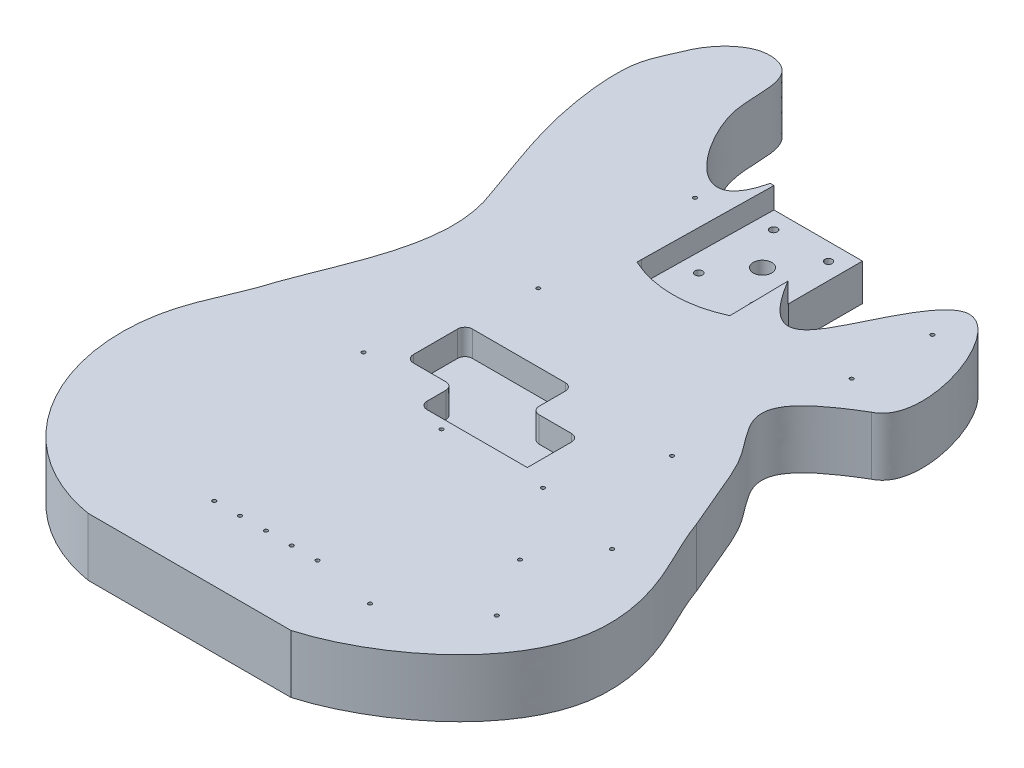
SolidWorks part; units mm, degrees
ref_plane "Front Plane" through (0, 0, 0) normal (0, 0, 1) x (1, 0, 0)
ref_plane "Top Plane" through (0, 0, 0) normal (0, 1, 0) x (1, 0, 0)
ref_plane "Right Plane" through (0, 0, 0) normal (1, 0, 0) x (0, 0, -1)
sketch "Sketch1" plane through (0, 0, 0) normal (0, 1, 0) x (1, 0, 0)
  line L0 (-31.75, 431.8) -> (31.75, 431.8)
  line L1 (-69.85, 0) -> (69.85, 0)
  line L2 (31.75, 431.8) -> (31.75, 381)
  line L3 (0, 431.8) -> (0, 0) construction
  spline S0 degree 3 poles (-69.85, 0) (-122.7459, 8.8946) (-170.3738, 68.3736) (-165.5312, 154.7593) (-147.8347, 185.8105) (-142.875, 203.2) knots 0 0 0 0 0.581043 0.783837 1 1 1 1
  spline S1 degree 3 poles (-142.875, 203.2) (-128.6398, 243.0991) (-104.4904, 285.9502) (-122.2248, 330.2) knots 0 0 0 0 1 1 1 1
  spline S2 degree 3 poles (-122.2248, 330.2) (-131.7635, 357.8566) (-146.2426, 392.3515) (-152.7726, 455.2781) (-144.5433, 471.0132) (-135.4704, 492.8612) (-120.6511, 508.7509) (-90.8297, 507.3178) (-88.3646, 481.7202) (-88.7047, 444.4419) (-43.0115, 384.6457) (-31.75, 431.8) knots 0 0 0 0 0.228271 0.373681 0.455315 0.473382 0.545352 0.564859 0.659458 0.744201 1 1 1 1
  spline S3 degree 3 poles (69.85, 0) (111.9348, 12.1111) (186.0145, 65.7497) (170.8416, 155.4983) (152.3381, 185.6263) (146.05, 203.2) knots 0 0 0 0 0.586136 0.784814 1 1 1 1
  spline S4 degree 3 poles (146.05, 203.2) (136.1599, 225.6504) (132.5896, 236.8474) (120.3836, 260.933) (109.5687, 273.3596) (96.5902, 297.0243) (109.0963, 311.9927) (139.7, 330.2) knots 0 0 0 0 0.33898 0.396393 0.554386 0.616722 1 1 1 1
  spline S5 degree 3 poles (139.7, 330.2) (166.4459, 342.892) (123.5038, 464.5308) (76.8127, 369.3895) (59.5093, 333.6668) (31.75, 381) knots 0 0 0 0 0.451982 0.679896 1 1 1 1
  point P5 (0, 412.75)
  point P7 (0, 0)
  point P10 (0, 50.8)
  point P11 (0, 101.6)
  point P12 (0, 152.4)
  point P13 (0, 177.8)
  point P15 (0, 203.2)
  point P17 (0, 254)
  point P18 (0, 279.4)
  point P19 (0, 330.2)
  point P20 (0, 406.4)
  point P21 (0, 381)
  point P22 (0, 482.6)
  point P23 (0, 508)
  point P24 (0, 457.2)
  point P25 (0, 355.6)
  point P38 (0, 422.275)
  dimension "D5" = 50.8
  dimension "D35" = 149.225
  dimension "D42" = 139.7
  dimension "D1" = 63.5
  dimension "D2" = 139.7
  dimension "D4" = 431.8
  dimension "D6" = 101.6
  dimension "D7" = 152.4
  dimension "D8" = 177.8
  dimension "D9" = 203.2
  dimension "D10" = 254
  dimension "D11" = 279.4
  dimension "D12" = 330.2
  dimension "D13" = 381
  dimension "D14" = 406.4
  dimension "D15" = 457.2
  dimension "D16" = 482.6
  dimension "D17" = 508
  dimension "D18" = 146.05
  dimension "D19" = 165.1
  dimension "D20" = 161.925
  dimension "D21" = 152.4
  dimension "D22" = 142.875
  dimension "D23" = 123.825
  dimension "D24" = 117.475
  dimension "D25" = 122.2248
  dimension "D26" = 139.7
  dimension "D27" = 146.05
  dimension "D28" = 149.225
  dimension "D29" = 139.7
  dimension "D30" = 107.95
  dimension "D31" = 88.9
  dimension "D32" = 85.725
  dimension "D33" = 6.35
  dimension "D34" = 53.975
  dimension "D36" = 174.625
  dimension "D37" = 168.275
  dimension "D38" = 157.1498
  dimension "D39" = 146.05
  dimension "D40" = 123.825
  dimension "D41" = 106.3498
  dimension "D43" = 355.6
  dimension "D44" = 422.275
  dimension "D45" = 146.05
  dimension "D46" = 114.3
  dimension "D47" = 82.55
  dimension "D48" = 66.675
extrude "Boss-Extrude1" add sketch "Sketch1" along normal blind 40.005
sketch "Sketch2" plane through (0, 40.005, 0) normal (0, 1, 0) x (1, 0, 0)
  line L0 (-29.21, 431.8) -> (31.75, 431.8)
  line L1 (31.75, 431.8) -> (-31.75, 431.8) construction
  line L2 (31.75, 381) -> (31.75, 431.8) construction
  line L3 (-29.21, 431.8) -> (-30.6832, 341.9475)
  line L4 (31.75, 431.8) -> (33.2232, 341.9475)
  line L5 (1.27, 431.8) -> (1.27, 340.7706) construction
  line L6 (-30.6832, 341.9475) -> (33.2232, 341.9475) construction
  line L7 (33.2232, 341.9475) -> (33.2232, 338.8995)
  line L8 (-30.6832, 341.9475) -> (-30.6832, 338.8995)
  line L9 (1.27, 407.1241) -> (1.27, 331.7875) construction
  arc A0 (-30.6832, 338.8995) -> (33.2232, 338.8995) centre (1.27, 407.1241) ccw
  point P13 (1.27, 341.9475)
  dimension "D5" = 7.112
  dimension "D1" = 60.96
  dimension "D2" = 89.8525
  dimension "D3" = 63.9064
  dimension "D4" = 3.048
extrude "Cut-Extrude1" cut sketch "Sketch2" against normal blind 14.605
sketch "Sketch3" plane through (0, 25.4, 0) normal (0, 1, 0) x (1, 0, 0)
  line L0 (1.27, 431.8) -> (1.27, 393.3952) construction
  line L1 (31.75, 431.8) -> (-29.21, 431.8) construction
  line L2 (31.75, 381) -> (31.75, 431.8) construction
  line L5 (33.2232, 341.9475) -> (32.6067, 379.5515) construction
  line L6 (-29.21, 431.8) -> (-30.6832, 341.9475) construction
  circle A0 centre (1.27, 393.3952) radius 6.35
  circle A1 centre (-17.526, 419.862) radius 2.54
  circle A2 centre (20.2692, 419.862) radius 2.54
  circle A3 centre (20.5972, 368.3) radius 2.54
  circle A4 centre (-17.5491, 368.3) radius 2.54
  point P0 (1.27, 399.7452)
  point P14 (-17.526, 422.402)
  point P15 (20.2692, 422.402)
  point P17 (22.8092, 419.862)
  point P19 (-14.986, 419.862)
  point P20 (23.1372, 368.3)
  point P21 (-20.0891, 368.3)
  point P22 (-17.5491, 370.84)
  point P23 (20.5972, 370.84)
  point P24 (-15.0091, 368.3)
  point P28 (18.0572, 368.3)
  dimension "D1" = 5.08
  dimension "D2" = 12.7
  dimension "D3" = 32.0548
  dimension "D4" = 9.398
  dimension "D5" = 8.9408
  dimension "D6" = 46.736
  dimension "D7" = 15.24
  dimension "D8" = 14.732
  dimension "D9" = 60.96
extrude "Cut-Extrude2" cut sketch "Sketch3" against normal through all
sketch "Sketch4" plane through (0, 40.005, 0) normal (0, 1, 0) x (1, 0, 0)
  line L0 (31.75, 431.8) -> (-29.21, 431.8) construction
  line L1 (-47.498, 242.316) -> (16.51, 242.316)
  line L2 (-52.578, 237.236) -> (-52.578, 206.756)
  line L3 (-47.498, 201.676) -> (-25.146, 201.676)
  line L4 (21.59, 237.236) -> (21.59, 219.202)
  line L5 (26.67, 214.122) -> (49.022, 214.122)
  line L6 (-20.066, 196.596) -> (-20.066, 183.642)
  line L7 (-14.986, 178.562) -> (54.102, 178.562)
  line L8 (54.102, 209.042) -> (54.102, 178.562)
  line L9 (31.75, 381) -> (31.75, 431.8) construction
  arc A0 (-20.066, 183.642) -> (-14.986, 178.562) centre (-14.986, 183.642) ccw
  arc A1 (49.022, 214.122) -> (54.102, 209.042) centre (49.022, 209.042) cw
  arc A2 (26.67, 214.122) -> (21.59, 219.202) centre (26.67, 219.202) cw
  arc A3 (-25.146, 201.676) -> (-20.066, 196.596) centre (-25.146, 196.596) cw
  arc A4 (-52.578, 206.756) -> (-47.498, 201.676) centre (-47.498, 206.756) ccw
  arc A5 (16.51, 242.316) -> (21.59, 237.236) centre (16.51, 237.236) cw
  arc A6 (-47.498, 242.316) -> (-52.578, 237.236) centre (-47.498, 237.236) ccw
  dimension "D7" = 5.08
  dimension "D1" = 35.56
  dimension "D2" = 74.168
  dimension "D3" = 63.754
  dimension "2.92" = 74.168
  dimension "D4" = 106.68
  dimension "D5" = 189.484
  dimension "D6" = 10.16
extrude "Cut-Extrude3" cut sketch "Sketch4" against normal blind 17.5514
sketch "Sketch5" plane through (0, 40.005, 0) normal (0, 1, 0) x (1, 0, 0)
  line L0 (-29.21, 431.8) -> (-30.6832, 341.9475) construction
  line L1 (16.51, 242.316) -> (-47.498, 242.316) construction
  line L2 (30.2922, 397.256) -> (30.2922, 83.7471) construction
  line L3 (-14.986, 178.562) -> (54.102, 178.562) construction
  circle A0 centre (-49.0828, 397.256) radius 1.27
  circle A1 centre (-49.0828, 289.306) radius 1.27
  circle A2 centre (-70.9903, 190.881) radius 1.27
  circle A3 centre (112.8422, 343.281) radius 1.27
  circle A4 centre (114.417, 397.256) radius 1.27
  circle A5 centre (96.9672, 235.331) radius 1.27
  circle A6 centre (131.8922, 159.131) radius 1.27
  circle A7 centre (131.8922, 79.756) radius 1.27
  circle A8 centre (81.0922, 43.2435) radius 1.27
  circle A9 centre (106.4922, 121.031) radius 1.27
  circle A10 centre (71.5672, 171.831) radius 1.27
  circle A11 centre (-33.8428, 50.8508) radius 1.27
  circle A12 centre (-16.0628, 50.8508) radius 1.27
  circle A13 centre (1.7172, 50.8508) radius 1.27
  circle A14 centre (19.4972, 50.8508) radius 1.27
  circle A15 centre (37.2772, 50.8508) radius 1.27
  circle A16 centre (1.7172, 171.831) radius 1.27
  point P2 (-47.8128, 397.256)
  point P5 (-49.0828, 395.986)
  point P42 (30.2922, 390.906)
  point P43 (30.2922, 365.506)
  point P44 (30.2922, 340.106)
  point P45 (30.2922, 314.706)
  point P46 (30.2922, 289.306)
  point P47 (30.2922, 263.906)
  point P48 (30.2922, 238.506)
  point P49 (30.2922, 213.106)
  point P50 (30.2922, 187.706)
  point P51 (30.2922, 162.306)
  point P52 (30.2922, 136.906)
  point P53 (30.2922, 111.506)
  point P54 (30.2922, 86.106)
  point P63 (1.7172, 52.1208)
  dimension "D1" = 2.54
  dimension "D27" = 17.78
  dimension "D2" = 18.034
  dimension "D3" = 153.67
  dimension "D4" = 79.375
  dimension "D5" = 79.375
  dimension "D6" = 6.35
  dimension "D8" = 25.4
  dimension "D9" = 101.2825
  dimension "D10" = 3.175
  dimension "D11" = 28.575
  dimension "D12" = 9.525
  dimension "D13" = 69.85
  dimension "D14" = 41.275
  dimension "D15" = 76.2
  dimension "D16" = 50.8
  dimension "D17" = 119.0625
  dimension "D18" = 101.6
  dimension "D19" = 82.55
  dimension "D20" = 101.6
  dimension "D21" = 3.175
  dimension "D22" = 66.675
  dimension "D23" = 3.175
  dimension "D24" = 3.175
  dimension "D25" = 82.55
  dimension "D26" = 84.1248
  dimension "D28" = 35.56
  dimension "D29" = 53.34
  dimension "D30" = 71.12
  dimension "D31" = 126.4412
  dimension "D7" = 13
extrude "Cut-Extrude4" cut sketch "Sketch5" against normal blind 17.78
